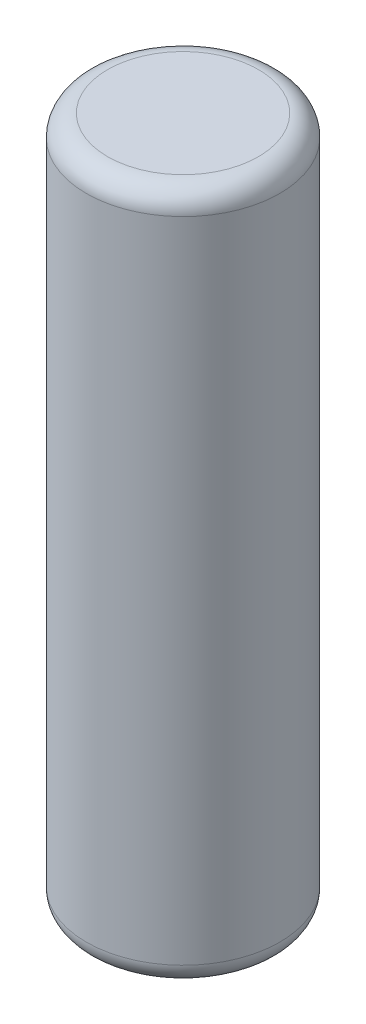
SolidWorks part; units mm, degrees
ref_plane "Front Plane" through (0, 0, 0) normal (0, 0, 1) x (1, 0, 0)
ref_plane "Top Plane" through (0, 0, 0) normal (0, 1, 0) x (1, 0, 0)
ref_plane "Right Plane" through (0, 0, 0) normal (1, 0, 0) x (0, 0, -1)
sketch "Sketch1" plane through (0, 0, 0) normal (0, 0, 1) x (1, 0, 0)
  line L0 (0, 0) -> (7.1, 0)
  line L1 (9.1, 2) -> (9.1, 63)
  line L2 (7.1, 65) -> (0, 65)
  line L3 (0, 65) -> (0, 0) construction
  line L4 (0, 0) -> (0, 65)
  arc A0 (7.1, 0) -> (9.1, 2) centre (7.1, 2) ccw
  arc A1 (9.1, 63) -> (7.1, 65) centre (7.1, 63) ccw
  point P7 (9.1, 0)
  point P10 (9.1, 65)
  dimension "D3" = 2
  dimension "D1" = 9.1
  dimension "D2" = 65
revolve "Revolve1" add sketch "Sketch1" angle 360 about L3
